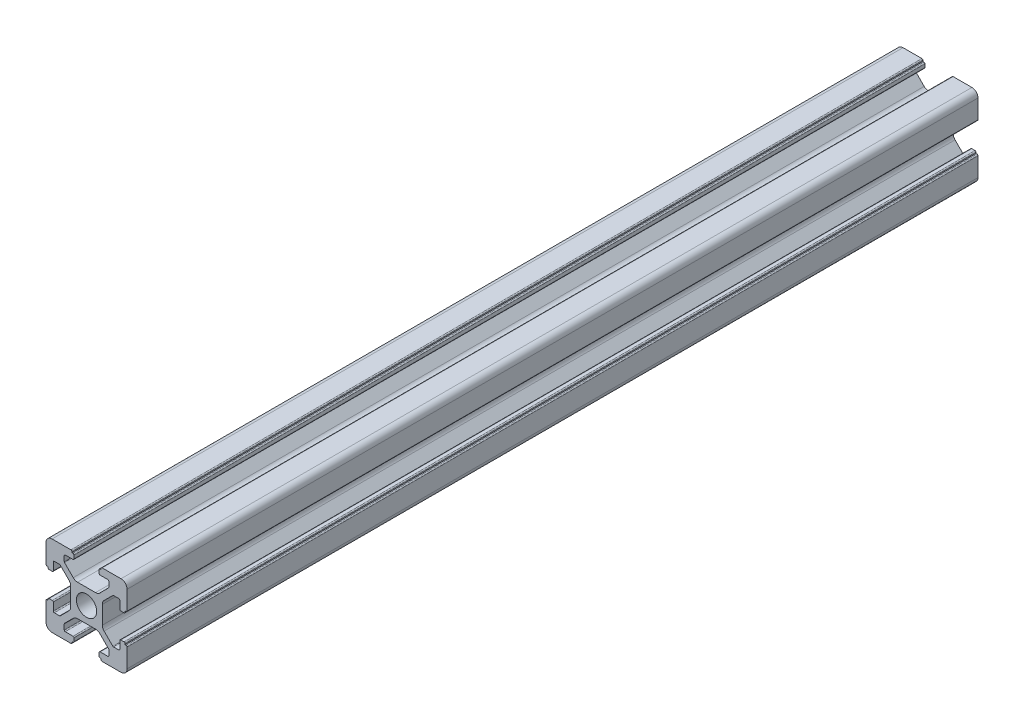
SolidWorks part; units mm, degrees
ref_plane "前视基准面" through (0, 0, 0) normal (0, 0, 1) x (1, 0, 0)
ref_plane "上视基准面" through (0, 0, 0) normal (0, 1, 0) x (1, 0, 0)
ref_plane "右视基准面" through (0, 0, 0) normal (1, 0, 0) x (0, 0, -1)
sketch "草图1" plane through (0, 0, 0) normal (0, 0, 1) x (1, 0, 0)
  line L0 (0, 0) -> (0, 5.5) construction
  line L1 (-8.5023, -10.0023) -> (-3.85, -10.0023)
  line L2 (-10.0023, -8.5023) -> (-10.0023, -3.85)
  line L3 (-8.5023, 10.0023) -> (-3.85, 10.0023)
  line L4 (10.0023, -8.5023) -> (10.0023, -3.85)
  line L5 (-10.0023, -10.0023) -> (10.0023, 10.0023) construction
  line L6 (-10.0023, 10.0023) -> (10.0023, -10.0023) construction
  line L7 (-2.218, -3.9) -> (2.218, -3.9)
  line L8 (-3.9, -2.218) -> (-3.9, 2.218)
  line L9 (-2.218, 3.9) -> (2.218, 3.9)
  line L10 (3.9, -2.218) -> (3.9, 2.218)
  line L11 (-3.9, -3.9) -> (3.9, 3.9) construction
  line L12 (-3.9, 3.9) -> (3.9, -3.9) construction
  line L13 (-5.25, -8.2) -> (-3.35, -8.2)
  line L14 (-8.2, -5.25) -> (-8.2, -3.35)
  line L15 (-5.25, 8.2) -> (-3.35, 8.2)
  line L16 (8.2, -5.25) -> (8.2, -3.35)
  line L17 (-8.2, -8.2) -> (8.2, 8.2) construction
  line L18 (-8.2, 8.2) -> (8.2, -8.2) construction
  line L19 (-7.95, 5.5) -> (-6.6642, 5.5)
  line L20 (0, 0) -> (5.5, 0) construction
  line L23 (-5.5, 7.95) -> (-5.5, 6.6642)
  line L26 (0, 0) -> (-0.5303, 0.5303)
  line L27 (3.2787, 4.3393) -> (5.4268, 6.4874)
  line L28 (0, 0) -> (0.5303, -0.5303)
  line L29 (5.5, 6.6642) -> (5.5, 7.95)
  line L30 (4.3393, 3.2787) -> (6.4874, 5.4268)
  line L31 (6.6642, 5.5) -> (7.95, 5.5)
  line L32 (4.3393, -3.2787) -> (6.4874, -5.4268)
  line L33 (3.2787, -4.3393) -> (5.4268, -6.4874)
  line L34 (-3.2787, -4.3393) -> (-5.4268, -6.4874)
  line L35 (-4.3393, -3.2787) -> (-6.4874, -5.4268)
  line L36 (-4.3393, 3.2787) -> (-6.4874, 5.4268)
  line L37 (-3.2787, 4.3393) -> (-5.4268, 6.4874)
  line L38 (3.1, -8.45) -> (3.1, -9.2523)
  line L39 (8.45, 3.1) -> (9.2523, 3.1)
  line L40 (-5.5, -6.6642) -> (-5.5, -7.95)
  line L41 (-6.6642, -5.5) -> (-7.95, -5.5)
  line L42 (5.5, -6.6642) -> (5.5, -7.95)
  line L43 (6.6642, -5.5) -> (7.95, -5.5)
  line L44 (9.2523, -3.1) -> (8.45, -3.1)
  line L46 (10.0023, 3.85) -> (10.0023, 8.5023)
  line L47 (8.2, 3.35) -> (8.2, 5.25)
  line L48 (-3.1, -9.2523) -> (-3.1, -8.45)
  line L49 (-8.45, -3.1) -> (-9.2523, -3.1)
  line L50 (-9.2523, 3.1) -> (-8.45, 3.1)
  line L51 (-3.1, 8.45) -> (-3.1, 9.2523)
  line L52 (3.1, 9.2523) -> (3.1, 8.45)
  line L53 (3.85, 10.0023) -> (8.5023, 10.0023)
  line L54 (3.35, 8.2) -> (5.25, 8.2)
  line L55 (-10.0023, 3.85) -> (-10.0023, 8.5023)
  line L56 (-8.2, 3.35) -> (-8.2, 5.25)
  line L57 (3.35, -8.2) -> (5.25, -8.2)
  line L58 (3.85, -10.0023) -> (8.5023, -10.0023)
  line L59 (9.7523, -3.6) -> (9.5023, -3.6)
  line L61 (9.7523, 3.6) -> (9.5023, 3.6)
  line L62 (9.5023, -3.6) -> (9.5023, -3.35)
  line L63 (3.6, -9.7523) -> (3.6, -9.5023)
  line L64 (3.35, -9.5023) -> (3.6, -9.5023)
  line L65 (9.5023, 3.35) -> (9.5023, 3.6)
  line L66 (-3.6, -9.5023) -> (-3.35, -9.5023)
  line L67 (-3.6, -9.7523) -> (-3.6, -9.5023)
  line L68 (-9.7523, -3.6) -> (-9.5023, -3.6)
  line L69 (-9.5023, -3.35) -> (-9.5023, -3.6)
  line L70 (-9.5023, 3.6) -> (-9.5023, 3.35)
  line L71 (-9.7523, 3.6) -> (-9.5023, 3.6)
  line L72 (-3.6, 9.7523) -> (-3.6, 9.5023)
  line L73 (-3.35, 9.5023) -> (-3.6, 9.5023)
  line L74 (3.6, 9.5023) -> (3.35, 9.5023)
  line L75 (3.6, 9.7523) -> (3.6, 9.5023)
  circle A0 centre (0, 0) radius 2.5
  arc A1 (10.0023, 8.5023) -> (8.5023, 10.0023) centre (8.5023, 8.5023) ccw
  arc A2 (8.5023, -10.0023) -> (10.0023, -8.5023) centre (8.5023, -8.5023) ccw
  arc A3 (-10.0023, -8.5023) -> (-8.5023, -10.0023) centre (-8.5023, -8.5023) ccw
  arc A4 (-10.0023, 8.5023) -> (-8.5023, 10.0023) centre (-8.5023, 8.5023) cw
  arc A5 (-9.5023, -3.35) -> (-9.2523, -3.1) centre (-9.2523, -3.35) cw
  arc A6 (-9.7523, -3.6) -> (-10.0023, -3.85) centre (-9.7523, -3.85) ccw
  arc A7 (-8.45, -3.1) -> (-8.2, -3.35) centre (-8.45, -3.35) cw
  arc A8 (-7.95, -5.5) -> (-8.2, -5.25) centre (-7.95, -5.25) cw
  arc A9 (-6.4874, -5.4268) -> (-6.6642, -5.5) centre (-6.6642, -5.25) cw
  arc A10 (-5.4268, -6.4874) -> (-5.5, -6.6642) centre (-5.25, -6.6642) ccw
  arc A11 (-5.5, -7.95) -> (-5.25, -8.2) centre (-5.25, -7.95) ccw
  arc A12 (-3.6, -9.7523) -> (-3.85, -10.0023) centre (-3.85, -9.7523) cw
  arc A13 (-3.35, -9.5023) -> (-3.1, -9.2523) centre (-3.35, -9.2523) ccw
  arc A14 (-3.1, -8.45) -> (-3.35, -8.2) centre (-3.35, -8.45) ccw
  arc A15 (3.1, -8.45) -> (3.35, -8.2) centre (3.35, -8.45) cw
  arc A16 (5.5, -7.95) -> (5.25, -8.2) centre (5.25, -7.95) cw
  arc A17 (5.4268, -6.4874) -> (5.5, -6.6642) centre (5.25, -6.6642) cw
  arc A18 (6.4874, -5.4268) -> (6.6642, -5.5) centre (6.6642, -5.25) ccw
  arc A19 (7.95, -5.5) -> (8.2, -5.25) centre (7.95, -5.25) ccw
  arc A20 (8.45, -3.1) -> (8.2, -3.35) centre (8.45, -3.35) ccw
  arc A21 (9.5023, -3.35) -> (9.2523, -3.1) centre (9.2523, -3.35) ccw
  arc A22 (9.7523, -3.6) -> (10.0023, -3.85) centre (9.7523, -3.85) cw
  arc A23 (3.35, -9.5023) -> (3.1, -9.2523) centre (3.35, -9.2523) cw
  arc A24 (3.6, -9.7523) -> (3.85, -10.0023) centre (3.85, -9.7523) ccw
  arc A25 (7.95, 5.5) -> (8.2, 5.25) centre (7.95, 5.25) cw
  arc A26 (8.2, 3.35) -> (8.45, 3.1) centre (8.45, 3.35) ccw
  arc A27 (9.5023, 3.35) -> (9.2523, 3.1) centre (9.2523, 3.35) cw
  arc A28 (9.7523, 3.6) -> (10.0023, 3.85) centre (9.7523, 3.85) ccw
  arc A29 (6.6642, 5.5) -> (6.4874, 5.4268) centre (6.6642, 5.25) ccw
  arc A30 (5.4268, 6.4874) -> (5.5, 6.6642) centre (5.25, 6.6642) ccw
  arc A31 (5.5, 7.95) -> (5.25, 8.2) centre (5.25, 7.95) ccw
  arc A32 (3.1, 8.45) -> (3.35, 8.2) centre (3.35, 8.45) ccw
  arc A33 (3.6, 9.7523) -> (3.85, 10.0023) centre (3.85, 9.7523) cw
  arc A34 (3.35, 9.5023) -> (3.1, 9.2523) centre (3.35, 9.2523) ccw
  arc A35 (-9.7523, 3.6) -> (-10.0023, 3.85) centre (-9.7523, 3.85) cw
  arc A36 (-9.5023, 3.35) -> (-9.2523, 3.1) centre (-9.2523, 3.35) ccw
  arc A37 (-8.45, 3.1) -> (-8.2, 3.35) centre (-8.45, 3.35) ccw
  arc A38 (-8.2, 5.25) -> (-7.95, 5.5) centre (-7.95, 5.25) cw
  arc A39 (-6.4874, 5.4268) -> (-6.6642, 5.5) centre (-6.6642, 5.25) ccw
  arc A40 (-5.4268, 6.4874) -> (-5.5, 6.6642) centre (-5.25, 6.6642) cw
  arc A41 (-5.5, 7.95) -> (-5.25, 8.2) centre (-5.25, 7.95) cw
  arc A42 (-3.1, 8.45) -> (-3.35, 8.2) centre (-3.35, 8.45) cw
  arc A43 (-3.1, 9.2523) -> (-3.35, 9.5023) centre (-3.35, 9.2523) ccw
  arc A44 (-3.6, 9.7523) -> (-3.85, 10.0023) centre (-3.85, 9.7523) ccw
  arc A45 (-4.3393, 3.2787) -> (-3.9, 2.218) centre (-5.4, 2.218) cw
  arc A46 (-3.2787, 4.3393) -> (-2.218, 3.9) centre (-2.218, 5.4) ccw
  arc A47 (3.2787, 4.3393) -> (2.218, 3.9) centre (2.218, 5.4) cw
  arc A48 (4.3393, 3.2787) -> (3.9, 2.218) centre (5.4, 2.218) ccw
  arc A49 (4.3393, -3.2787) -> (3.9, -2.218) centre (5.4, -2.218) cw
  arc A50 (3.2787, -4.3393) -> (2.218, -3.9) centre (2.218, -5.4) ccw
  arc A51 (-4.3393, -3.2787) -> (-3.9, -2.218) centre (-5.4, -2.218) ccw
  arc A52 (-2.218, -3.9) -> (-3.2787, -4.3393) centre (-2.218, -5.4) ccw
  point P0 (0, 0)
  point P7 (10.0023, 0)
  point P62 (0, 0)
  point P76 (0, 0)
  point P92 (-8.2, -5.5)
  point P99 (0, 0)
  point P106 (-5.5, -8.2)
  point P117 (5.5, -8.2)
  point P124 (8.2, -5.5)
  point P137 (8.2, 5.5)
  point P140 (8.2, 3.1)
  point P147 (6.5607, 5.5)
  point P152 (5.5, 8.2)
  point P167 (-8.2, 5.5)
  point P174 (-5.5, 8.2)
  dimension "D1" = 1.5
  dimension "D5" = 0.25
  dimension "D6" = 1.5
  dimension "D2" = 4
  dimension "D3" = 4
  dimension "D4" = 4
extrude "凸台-拉伸1" add sketch "草图1" along normal blind 1220 contours A52 L7 A50 L33 A17 L42 A16 L57 A15 L38 A23 L64 L63 A24 L58 A2 L4 A22 L59 L62 A21 L44 A20 L16 A19 L43 A18 L32 A49 L10 A48 L30 A29 L31 A25 L47 A26 L39 A27 L65 L61 A28 L46 A1 L53 A33 L75 L74 A34 L52 A32
ref_plane "Plane1" through (0, 0, 1010) normal (0, 0, 1) x (1, 0, 0)
sketch "Sketch1" plane through (0, 0, 1010) normal (0, 0, 1) x (1, 0, 0)
  circle A0 centre (0, 0) radius 16.7715
extrude "Cut-Extrude1" cut sketch "Sketch1" against normal through all
ref_plane "CenterPlane" through (0, 0, 1115) normal (0, 0, 1) x (1, 0, 0)
